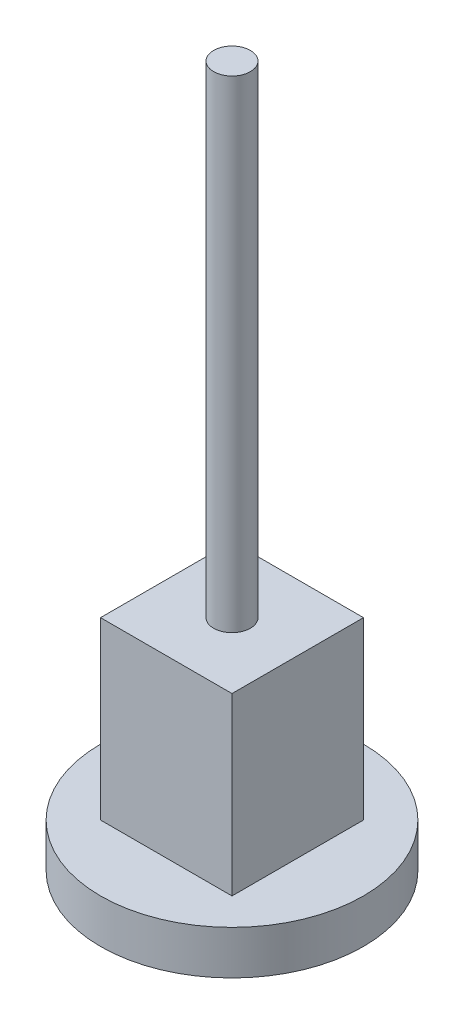
SolidWorks part; units mm, degrees
ref_plane "Front Plane" through (0, 0, 0) normal (0, 0, 1) x (1, 0, 0)
ref_plane "Top Plane" through (0, 0, 0) normal (0, 1, 0) x (1, 0, 0)
ref_plane "Right Plane" through (0, 0, 0) normal (1, 0, 0) x (0, 0, -1)
sketch "Sketch1" plane through (0, 0, 0) normal (0, 1, 0) x (1, 0, 0)
  circle A0 centre (0, 0) radius 30
  dimension "D1" = 60
extrude "Boss-Extrude1" add sketch "Sketch1" along normal blind 10 contours A0
sketch "Sketch2" plane through (0, 10, 0) normal (0, 1, 0) x (1, 0, 0)
  line L1 (-15, 15) -> (15, 15)
  line L2 (-15, 15) -> (-15, -15)
  line L3 (-15, -15) -> (15, -15)
  line L4 (15, 15) -> (15, -15)
  line L5 (-15, 15) -> (15, -15) construction
  line L6 (-15, -15) -> (15, 15) construction
  point P0 (0, 0)
  dimension "D1" = 30
  dimension "D2" = 30
extrude "Boss-Extrude2" add sketch "Sketch2" along normal blind 40
sketch "Sketch3" plane through (0, 50, 0) normal (0, 1, 0) x (1, 0, 0)
  circle A0 centre (0, 0) radius 4.197
extrude "Boss-Extrude3" add sketch "Sketch3" along normal blind 110 contours A0
